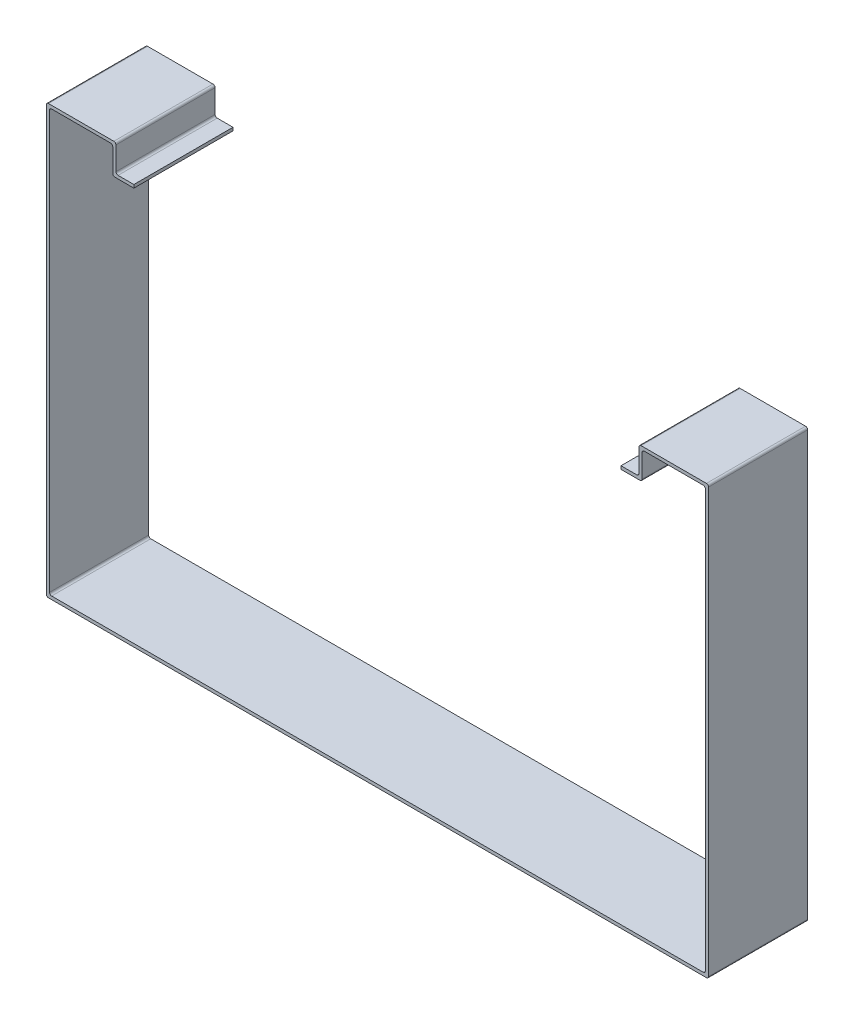
SolidWorks part; units mm, degrees
ref_plane "前视基准面" through (0, 0, 0) normal (0, 0, 1) x (1, 0, 0)
ref_plane "上视基准面" through (0, 0, 0) normal (0, 1, 0) x (1, 0, 0)
ref_plane "右视基准面" through (0, 0, 0) normal (1, 0, 0) x (0, 0, -1)
sketch "草图1" plane through (0, 0, 0) normal (0, 0, 1) x (1, 0, 0)
  line L0 (18.6395, 45.7366) -> (46.6395, 45.7366)
  line L1 (47.6395, 44.7366) -> (47.6395, -153.2634)
  line L2 (46.6395, -154.2634) -> (-262.3605, -154.2634)
  line L3 (48.1395, -155.7634) -> (-263.8605, -155.7634)
  line L4 (-264.8605, 46.2366) -> (-264.8605, -154.7634)
  line L5 (-232.8605, 47.2366) -> (-263.8605, 47.2366)
  line L6 (-231.8605, 35.2366) -> (-231.8605, 46.2366)
  line L7 (17.6395, 44.7366) -> (17.6395, 33.7366)
  line L8 (16.6395, 32.7366) -> (7.6395, 32.7366)
  line L9 (7.6395, 32.7366) -> (7.6395, 34.2366)
  line L10 (7.6395, 34.2366) -> (15.1395, 34.2366)
  line L11 (16.1395, 35.2366) -> (16.1395, 46.2366)
  line L12 (17.1395, 47.2366) -> (48.1395, 47.2366)
  line L13 (49.1395, 46.2366) -> (49.1395, -154.7634)
  line L14 (-107.8605, -154.2634) -> (-107.8605, 0) construction
  line L15 (-223.3605, 34.2366) -> (-230.8605, 34.2366)
  line L16 (-223.3605, 32.7366) -> (-223.3605, 34.2366)
  line L17 (-232.3605, 32.7366) -> (-223.3605, 32.7366)
  line L18 (-233.3605, 44.7366) -> (-233.3605, 33.7366)
  line L19 (-263.3605, 44.7366) -> (-263.3605, -153.2634)
  line L20 (-234.3605, 45.7366) -> (-262.3605, 45.7366)
  arc A0 (17.6395, 33.7366) -> (16.6395, 32.7366) centre (16.6395, 33.7366) cw
  arc A1 (16.1395, 35.2366) -> (15.1395, 34.2366) centre (15.1395, 35.2366) cw
  arc A2 (17.6395, 44.7366) -> (18.6395, 45.7366) centre (18.6395, 44.7366) cw
  arc A3 (16.1395, 46.2366) -> (17.1395, 47.2366) centre (17.1395, 46.2366) cw
  arc A4 (48.1395, 47.2366) -> (49.1395, 46.2366) centre (48.1395, 46.2366) cw
  arc A5 (46.6395, 45.7366) -> (47.6395, 44.7366) centre (46.6395, 44.7366) cw
  arc A6 (49.1395, -154.7634) -> (48.1395, -155.7634) centre (48.1395, -154.7634) cw
  arc A7 (46.6395, -154.2634) -> (47.6395, -153.2634) centre (46.6395, -153.2634) ccw
  arc A8 (-262.3605, -154.2634) -> (-263.3605, -153.2634) centre (-262.3605, -153.2634) cw
  arc A9 (-264.8605, -154.7634) -> (-263.8605, -155.7634) centre (-263.8605, -154.7634) ccw
  arc A10 (-262.3605, 45.7366) -> (-263.3605, 44.7366) centre (-262.3605, 44.7366) ccw
  arc A11 (-263.8605, 47.2366) -> (-264.8605, 46.2366) centre (-263.8605, 46.2366) ccw
  arc A12 (-231.8605, 46.2366) -> (-232.8605, 47.2366) centre (-232.8605, 46.2366) ccw
  arc A13 (-233.3605, 44.7366) -> (-234.3605, 45.7366) centre (-234.3605, 44.7366) ccw
  arc A14 (-231.8605, 35.2366) -> (-230.8605, 34.2366) centre (-230.8605, 35.2366) ccw
  arc A15 (-233.3605, 33.7366) -> (-232.3605, 32.7366) centre (-232.3605, 33.7366) ccw
  point P55 (-107.8605, -155.7634)
  dimension "D1" = 1
  dimension "D2" = 1
  dimension "D3" = 1
  dimension "D4" = 1
extrude "凸台-拉伸1" add sketch "草图1" along normal blind 47
